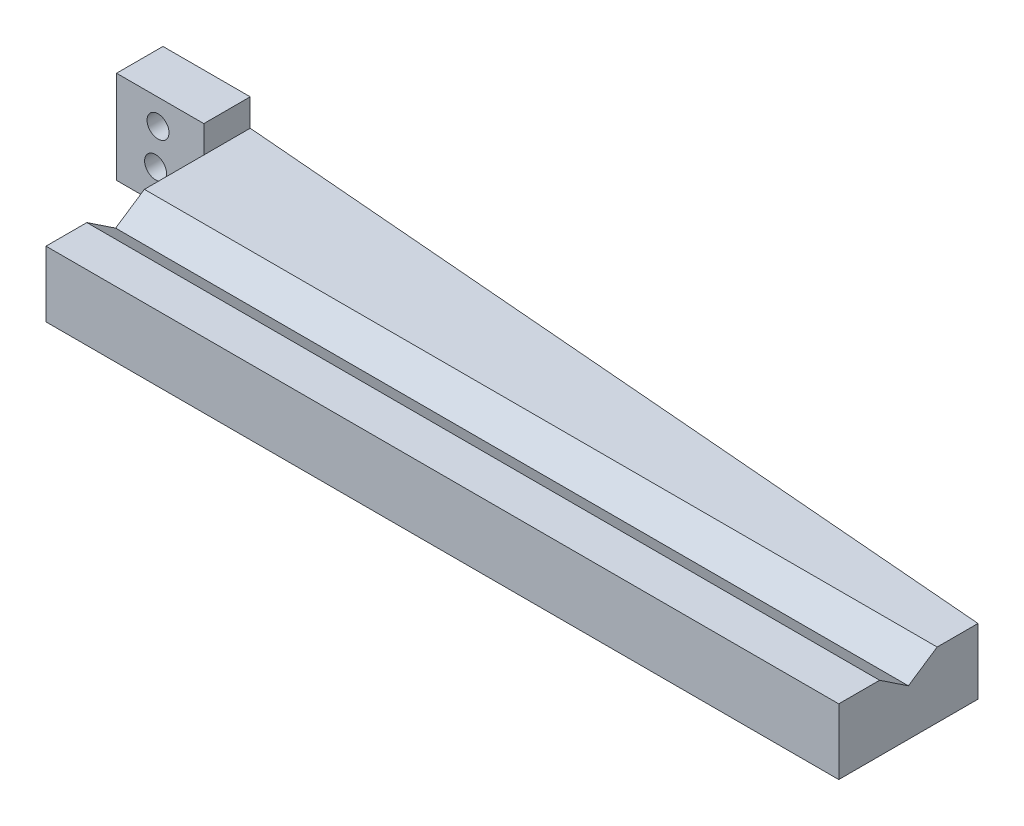
SolidWorks part; units mm, degrees
ref_plane "Front Plane" through (0, 0, 0) normal (0, 0, 1) x (1, 0, 0)
ref_plane "Top Plane" through (0, 0, 0) normal (0, 1, 0) x (1, 0, 0)
ref_plane "Right Plane" through (0, 0, 0) normal (1, 0, 0) x (0, 0, -1)
sketch "Sketch1" plane through (0, 0, 0) normal (0, 1, 0) x (1, 0, 0)
  line L0 (0, 0) -> (0, 12.7)
  line L1 (0, 12.7) -> (11.938, 12.7)
  line L2 (11.938, 12.7) -> (11.938, 19.05)
  line L3 (11.938, 19.05) -> (-108.458, 19.05)
  line L4 (-108.458, 19.05) -> (-108.458, 0)
  line L5 (-108.458, 0) -> (0, 0)
  dimension "D1" = 11.938
  dimension "D2" = 6.35
  dimension "D3" = 12.7
  dimension "D4" = 108.458
extrude "Boss-Extrude1" add sketch "Sketch1" along normal blind 6.35
sketch "Sketch2" plane through (-108.458, 0, 0) normal (-1, 0, 0) x (0, 0, 1)
  line L0 (-9.525, 6.35) -> (-13.462, 8.9747)
  line L1 (-19.05, 6.35) -> (0, 6.35) construction
  line L2 (-13.462, 8.9747) -> (-13.462, 6.35)
  line L3 (-13.462, 6.35) -> (-5.588, 6.35)
  line L4 (-5.588, 6.35) -> (-5.588, 8.9747)
  line L5 (-5.588, 8.9747) -> (-9.525, 6.35)
  line L6 (-13.462, 8.9747) -> (-19.05, 8.9747)
  line L7 (-19.05, 8.9747) -> (-19.05, 6.35)
  line L8 (-19.05, 6.35) -> (-13.462, 6.35)
  line L9 (-5.588, 8.9747) -> (0, 8.9747)
  line L10 (0, 8.9747) -> (0, 6.35)
  line L11 (0, 6.35) -> (-5.588, 6.35)
  line M6 (0, 6.35) -> (-19.05, 6.35)
  dimension "D1" = 112.62
  dimension "D2" = 7.874
  dimension "D3" = 3.937
extrude "Boss-Extrude2" add sketch "Sketch2" against normal up to surface (108.458 mm away) contours L10 L9 L4 M6 | L6 L7 L2 M6 | L4 L5 M6 | L0 L2 M6 up to face at (0, 3.175, -6.35)
sketch "Sketch3" plane through (0, 6.35, 0) normal (0, 1, 0) x (1, 0, 0)
  line L4 (11.938, 19.05) -> (0, 19.05)
  line L5 (0, 19.05) -> (0, 12.7)
  line L6 (0, 12.7) -> (11.938, 12.7)
  line L7 (11.938, 12.7) -> (11.938, 19.05)
  line L8 (11.938, 19.05) -> (0, 19.05)
  line L9 (0, 19.05) -> (0, 12.7)
  line L10 (0, 12.7) -> (11.938, 12.7)
  line L11 (11.938, 12.7) -> (11.938, 19.05)
  dimension "D1" = 0
extrude "Boss-Extrude3" add sketch "Sketch3" along normal blind 6.35
sketch "Sketch4" plane through (0, 0, -19.05) normal (0, 0, -1) x (-1, 0, 0)
  circle A0 centre (-6.5997, 4.2373) radius 1.5
  circle A1 centre (-6.2636, 9.2348) radius 1.5
  point P4 (-6.5997, 4.2373)
  dimension "D1" = 3
  dimension "D2" = 3
extrude "Cut-Extrude1" cut sketch "Sketch4" against normal blind 6.35
ref_plane "Plane1" through (-54.229, 0, 0) normal (-1, 0, 0) x (0, 0, 1)
mirror "Mirror1" about plane through (-54.229, 0, 0) normal (-1, 0, 0) of "Boss-Extrude1", "Boss-Extrude3", "Cut-Extrude1"
sketch "Sketch5" plane through (0, 0, -19.05) normal (0, 0, -1) x (-1, 0, 0)
  line L1 (0, 12.7) -> (-24.2009, 12.7)
  line L2 (0, 12.7) -> (0, -31.2145)
  line L3 (0, -31.2145) -> (-24.2009, -31.2145)
  line L4 (-24.2009, 12.7) -> (-24.2009, -31.2145)
extrude "Cut-Extrude2" cut sketch "Sketch5" against normal blind 6.35
sketch "Sketch6" plane through (0, 0, 0) normal (0, -1, 0) x (1, 0, 0)
  line L0 (-108.458, -19.05) -> (-108.458, -21.59)
  line L1 (-108.458, -27.94) -> (-120.396, -27.94)
  line L2 (-120.396, -27.94) -> (-120.396, -21.59)
  line L3 (-120.396, -21.59) -> (-108.458, -21.59)
  line L4 (-108.458, -27.94) -> (0, -19.05)
  line L7 (-108.458, -19.05) -> (-108.458, -16.6779)
  line L8 (-108.458, -16.6779) -> (0, -16.6779)
  line L9 (0, 0) -> (0, -19.05) construction
  line L10 (0, -16.6779) -> (0, -19.05)
  line L11 (-108.458, -12.7) -> (-120.396, -12.7) construction
  dimension "D1" = 8.89
  dimension "D2" = 6.35
extrude "Boss-Extrude8" add sketch "Sketch6" against normal up to surface (12.7 mm away) up to face at (-114.427, 12.7, -15.875)
sketch "Sketch7" plane through (0, 0, -27.94) normal (0, 0, -1) x (-1, 0, 0)
  circle A0 centre (114.7216, 9.2348) radius 1.5 construction
  circle A1 centre (115.0577, 4.2373) radius 1.5 construction
  circle A2 centre (114.7216, 9.2348) radius 1.5
  circle A3 centre (115.0577, 4.2373) radius 1.5
extrude "Cut-Extrude3" cut sketch "Sketch7" against normal blind 33.02
sketch "Sketch8" plane through (0, 12.7, 0) normal (0, 1, 0) x (1, 0, 0)
  line L1 (-108.458, 12.7) -> (-120.396, 12.7)
  line L2 (-108.458, 12.7) -> (-108.458, 19.05)
  line L3 (-108.458, 19.05) -> (-120.396, 19.05)
  line L4 (-120.396, 12.7) -> (-120.396, 19.05)
extrude "Cut-Extrude4" cut sketch "Sketch8" against normal blind 33.02
sketch "Sketch9" plane through (0, 12.7, 0) normal (0, 1, 0) x (1, 0, 0)
  line L0 (-108.458, 27.94) -> (-108.458, 21.59)
  line L7 (-108.458, 21.59) -> (-108.458, 16.6779)
  line L8 (-108.458, 16.6779) -> (0, 16.6779)
  line L9 (0, 16.6779) -> (0, 19.05)
  line L10 (0, 19.05) -> (-108.458, 27.94)
  line L11 (-108.458, 27.94) -> (-120.396, 27.94)
  line L12 (-120.396, 27.94) -> (-120.396, 21.59)
  line L13 (-120.396, 21.59) -> (-108.458, 21.59)
  line L14 (-108.458, 21.59) -> (-108.458, 16.6779)
  line L15 (-108.458, 16.6779) -> (0, 16.6779)
  line L16 (0, 16.6779) -> (0, 19.05)
  line L17 (0, 19.05) -> (-108.458, 27.94)
  dimension "D1" = 0
extrude "Cut-Extrude5" cut sketch "Sketch9" against normal up to surface (3.7253 mm away) up to face at (-54.229, 8.9747, -15.07)
equation "\"D3@Sketch2\"=\"D2@Sketch2\"/2"
